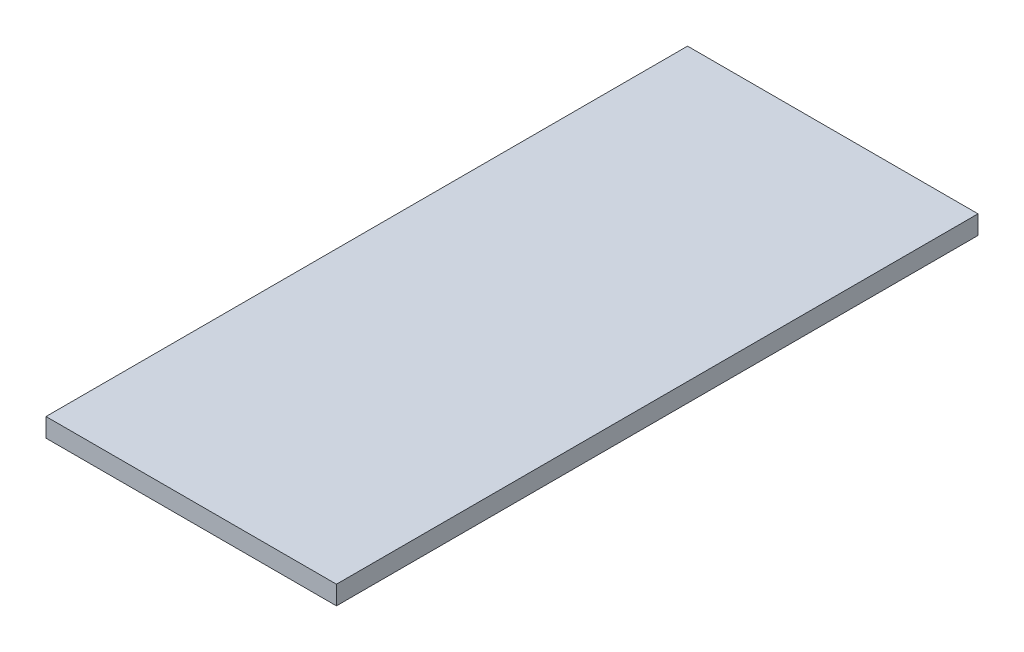
SolidWorks part; units mm, degrees
ref_plane "Front Plane" through (0, 0, 0) normal (0, 0, 1) x (1, 0, 0)
ref_plane "Top Plane" through (0, 0, 0) normal (0, 1, 0) x (1, 0, 0)
ref_plane "Right Plane" through (0, 0, 0) normal (1, 0, 0) x (0, 0, -1)
sketch "Sketch2" plane through (0, 0, 0) normal (0, 1, 0) x (1, 0, 0)
  line L0 (-56.593, 1190.0811) -> (-56.593, -4.9189)
  line L1 (-56.593, -4.9189) -> (484.407, -4.9189)
  line L2 (484.407, -4.9189) -> (484.407, 1190.0811)
  line L3 (484.407, 1190.0811) -> (-56.593, 1190.0811)
extrude "Boss-Extrude1" add sketch "Sketch2" along normal blind 35
